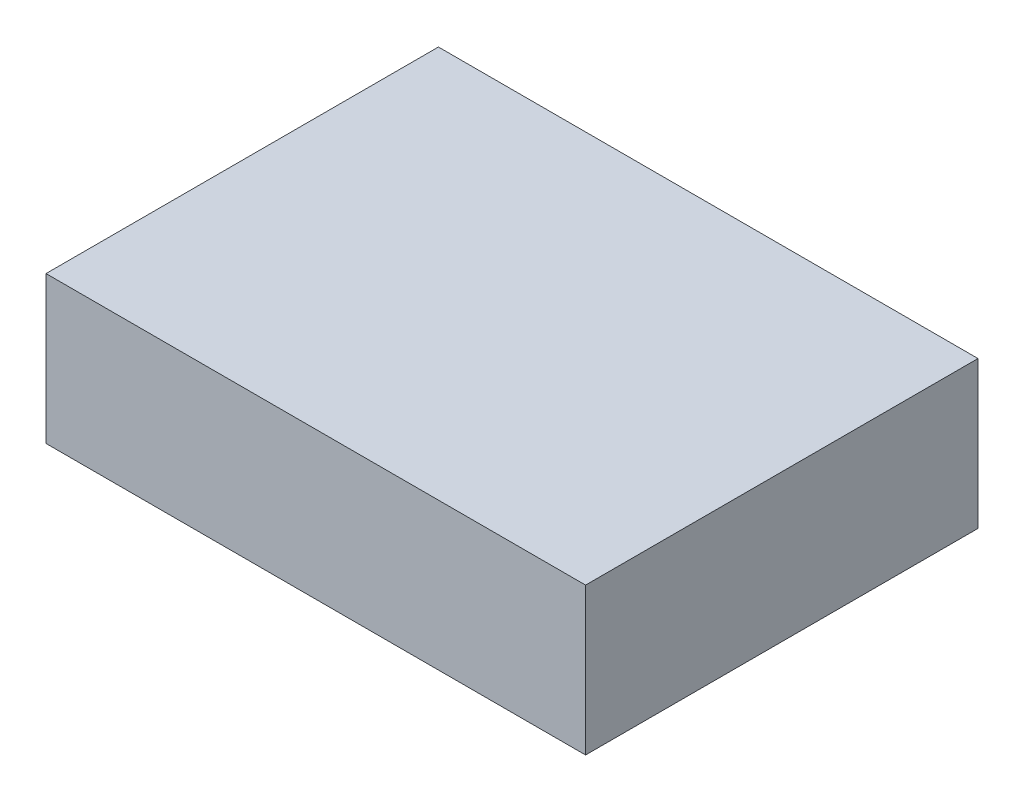
SolidWorks part; units mm, degrees
ref_plane "Front Plane" through (0, 0, 0) normal (0, 0, 1) x (1, 0, 0)
ref_plane "Top Plane" through (0, 0, 0) normal (0, 1, 0) x (1, 0, 0)
ref_plane "Right Plane" through (0, 0, 0) normal (1, 0, 0) x (0, 0, -1)
sketch "Sketch1" plane through (0, 0, 0) normal (0, 1, 0) x (1, 0, 0)
  line L1 (27.5, 20) -> (-27.5, 20)
  line L2 (27.5, 20) -> (27.5, -20)
  line L3 (27.5, -20) -> (-27.5, -20)
  line L4 (-27.5, 20) -> (-27.5, -20)
  line L5 (27.5, 20) -> (-27.5, -20) construction
  line L6 (27.5, -20) -> (-27.5, 20) construction
  point P0 (0, 0)
  dimension "D1" = 55
  dimension "D2" = 40
extrude "Boss-Extrude1" add sketch "Sketch1" along normal blind 15
sketch "Sketch2" plane through (0, 0, 0) normal (0, -1, 0) x (1, 0, 0)
  line L1 (-23.5, -16) -> (23.5, -16) construction
  line L2 (-23.5, -16) -> (-23.5, 16) construction
  line L3 (-23.5, 16) -> (23.5, 16) construction
  line L4 (23.5, -16) -> (23.5, 16) construction
  line L5 (-23.5, -16) -> (23.5, 16) construction
  line L6 (-23.5, 16) -> (23.5, -16) construction
  point P0 (0, 0)
  dimension "D1" = 47
  dimension "D2" = 32
hole_wizard "M1.2x0.25 Tapped Hole1" positions "Sketch3" profile "Sketch4" tap size "M1.2x0.25" standard "ANSI Metric"
sketch "Sketch3" plane through (0, 0, 0) normal (0, -1, 0) x (-1, 0, 0)
  point P0 (-23.5, -16)
  point P3 (23.5, 16)
sketch "Sketch4" plane through (23.5, 0, 16) normal (1, 0, 0) x (0, 0, -1)
  line L0 (0, 0) -> (0, 8.7854)
  line L1 (0, 8.7854) -> (0.475, 8.5)
  line L2 (0.475, 8.5) -> (0.475, 0)
  line L5 (0.475, 0) -> (0, 0)
  line L10 (0, 8.7854) -> (-0.475, 8.5) construction
  line L11 (0, -6.35) -> (0, 107.95) construction
  dimension "Tap Drill Dia." = 0.95
  dimension "Tap Drill Depth" = 8.5
  dimension "Drill Angle" = 118
